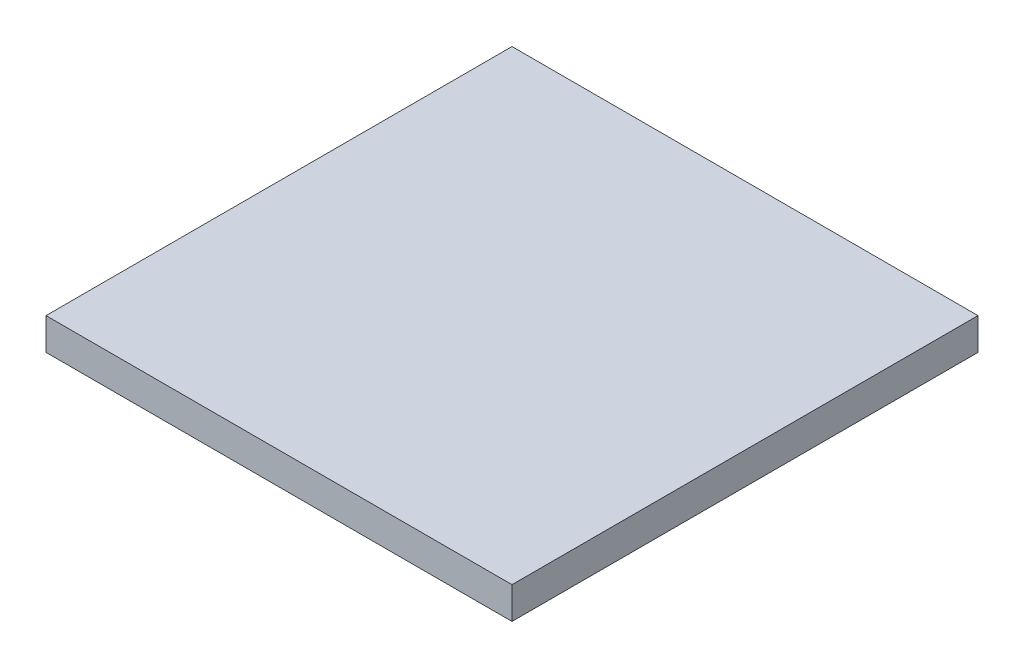
SolidWorks part; units mm, degrees
ref_plane "Front Plane" through (0, 0, 0) normal (0, 0, 1) x (1, 0, 0)
ref_plane "Top Plane" through (0, 0, 0) normal (0, 1, 0) x (1, 0, 0)
ref_plane "Right Plane" through (0, 0, 0) normal (1, 0, 0) x (0, 0, -1)
sketch "Sketch1" plane through (0, 0, 0) normal (0, 1, 0) x (1, 0, 0)
  line L1 (-24.4526, 18.7044) -> (25.5474, 18.7044)
  line L2 (-24.4526, 18.7044) -> (-24.4526, -31.2956)
  line L3 (-24.4526, -31.2956) -> (25.5474, -31.2956)
  line L4 (25.5474, 18.7044) -> (25.5474, -31.2956)
  dimension "D1" = 50
  dimension "D2" = 50
extrude "Boss-Extrude1" add sketch "Sketch1" along normal blind 3.42
